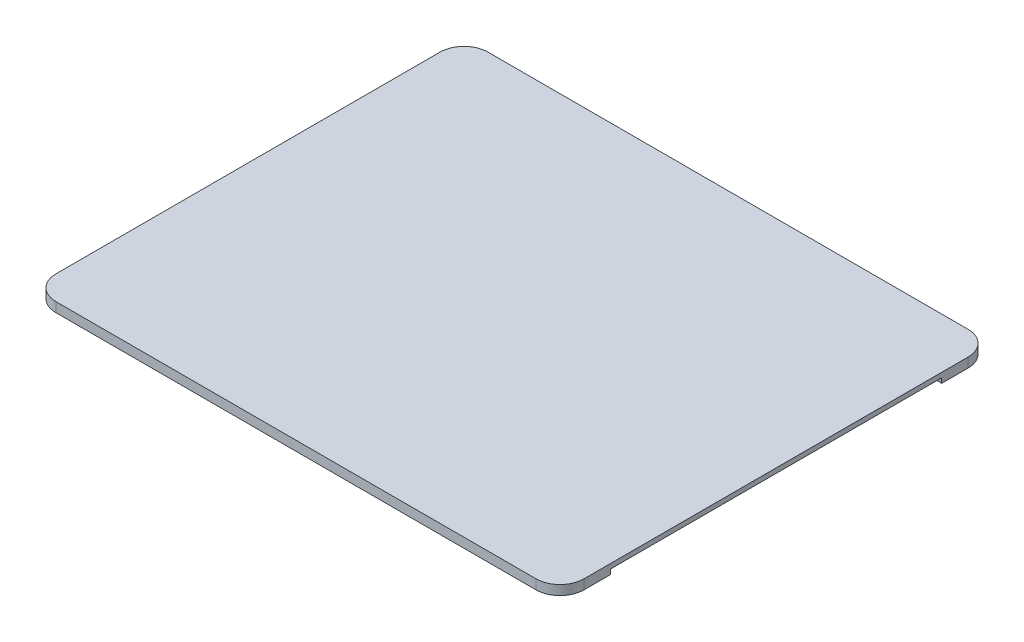
SolidWorks part; units mm, degrees
ref_plane "Front Plane" through (0, 0, 0) normal (0, 0, 1) x (1, 0, 0)
ref_plane "Top Plane" through (0, 0, 0) normal (0, 1, 0) x (1, 0, 0)
ref_plane "Right Plane" through (0, 0, 0) normal (1, 0, 0) x (0, 0, -1)
sketch "Sketch1" plane through (0, 0, 0) normal (0, 1, 0) x (1, 0, 0)
  line L1 (-49.5, 39.5) -> (49.5, 39.5)
  line L2 (-49.5, 39.5) -> (-49.5, -39.5)
  line L3 (-49.5, -39.5) -> (49.5, -39.5)
  line L4 (49.5, 39.5) -> (49.5, -39.5)
  line L5 (-49.5, 39.5) -> (49.5, -39.5) construction
  line L6 (-49.5, -39.5) -> (49.5, 39.5) construction
  point P0 (0, 0)
  dimension "D1" = 99
  dimension "D2" = 79
extrude "Boss-Extrude1" add sketch "Sketch1" along normal blind 3
fillet "Fillet1" radius 5 4 edges at (49.5, 1.5, -39.5) (-49.5, 1.5, -39.5) (-49.5, 1.5, 39.5) (49.5, 1.5, 39.5)
fillet "Fillet2" radius 1 8 edges at (-48.0355, 0, 38.0355) (-49.5, 0, 0) (-48.0355, 0, -38.0355) (0, 0, 39.5) (48.0355, 0, 38.0355) (49.5, 0, 0) (48.0355, 0, -38.0355) (0, 0, -39.5)
sketch "Sketch2" plane through (0, 3, 0) normal (0, 1, 0) x (1, 0, 0)
  line L1 (-55, 45) -> (55, 45)
  line L2 (-55, 45) -> (-55, -45)
  line L3 (-55, -45) -> (55, -45)
  line L4 (55, 45) -> (55, -45)
  line L5 (-55, 45) -> (55, -45) construction
  line L6 (-55, -45) -> (55, 45) construction
  point P0 (0, 0)
  dimension "D1" = 110
  dimension "D2" = 90
extrude "Boss-Extrude2" add sketch "Sketch2" along normal blind 2
fillet "Fillet3" radius 5 4 edges at (-55, 4, -45) (-55, 4, 45) (55, 4, -45) (55, 4, 45)
sketch "Sketch3" plane through (55, 0, 0) normal (1, 0, 0) x (0, 0, -1)
  line L0 (0, 5) -> (0, 3) construction
  line L1 (-34.5, 3) -> (34.5, 3)
  line L2 (-34.5, 3) -> (-34.5, 4)
  line L3 (-34.5, 4) -> (34.5, 4)
  line L4 (34.5, 3) -> (34.5, 4)
  line L6 (-40, 5) -> (40, 5) construction
  line L7 (0, 4) -> (0, 3) construction
  dimension "D1" = 1
  dimension "D2" = 69
extrude "Cut-Extrude1" cut sketch "Sketch3" against normal blind 3
ref_plane "Plane1" through (0, 0, 0) normal (1, 0, 0) x (0, 0, -1)
mirror "Mirror1" about plane through (0, 0, 0) normal (1, 0, 0) of "Cut-Extrude1"
